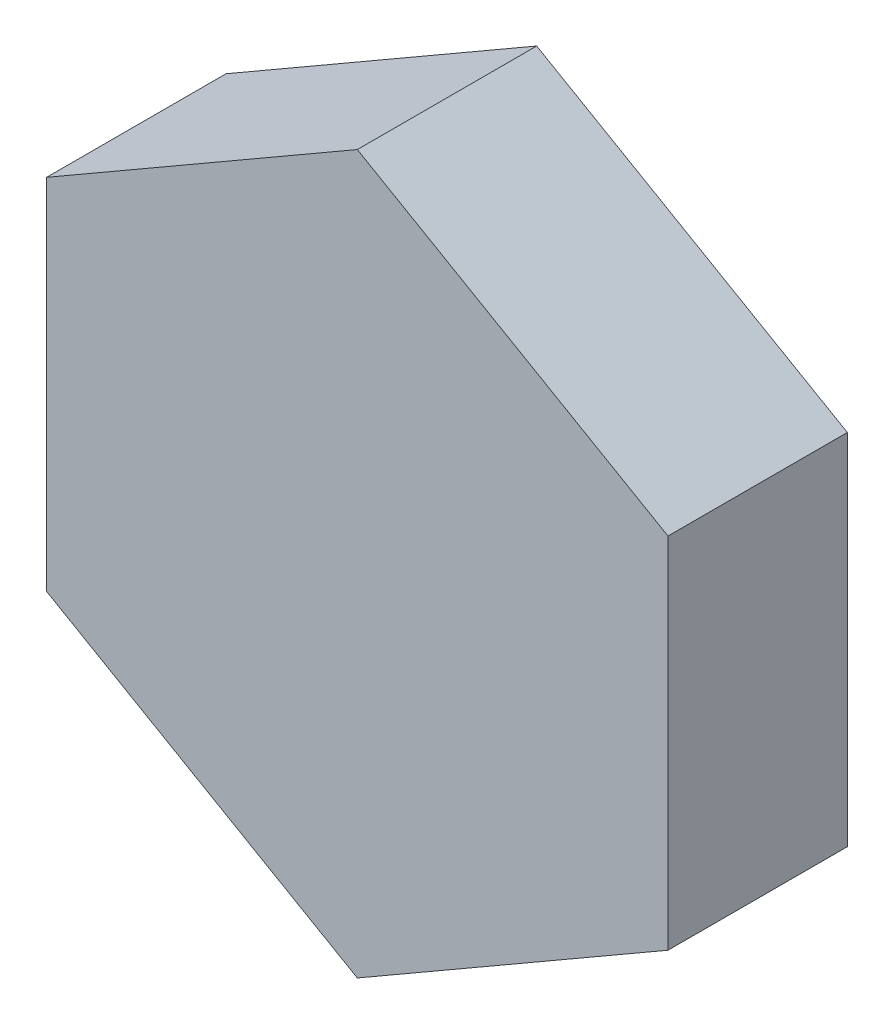
SolidWorks part; units mm, degrees
ref_plane "Front" through (0, 0, 0) normal (0, 0, 1) x (1, 0, 0)
ref_plane "Top" through (0, 0, 0) normal (0, 1, 0) x (1, 0, 0)
ref_plane "Right" through (0, 0, 0) normal (1, 0, 0) x (0, 0, -1)
sketch "Sketch1" plane through (0, 0, 0) normal (0, 0, 1) x (1, 0, 0)
  line L1 (43.9941, -25.4) -> (43.9941, 25.4)
  line L2 (43.9941, 25.4) -> (0, 50.8)
  line L3 (0, 50.8) -> (-43.9941, 25.4)
  line L4 (-43.9941, 25.4) -> (-43.9941, -25.4)
  line L5 (-43.9941, -25.4) -> (0, -50.8)
  line L6 (0, -50.8) -> (43.9941, -25.4)
  circle A0 centre (0, 0) radius 43.9941 construction
  dimension "D1" = 50.8
  dimension "D2" = 101.6
extrude "Boss-Extrude1" add sketch "Sketch1" along normal blind 25.4
